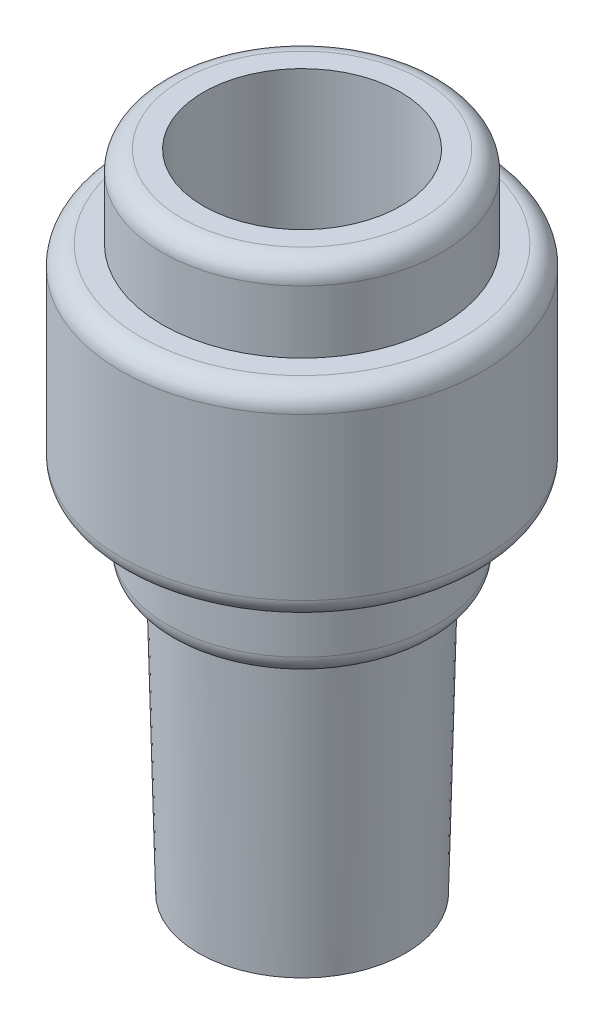
SolidWorks part; units mm, degrees
ref_plane "Front Plane" through (0, 0, 0) normal (0, 0, 1) x (1, 0, 0)
ref_plane "Top Plane" through (0, 0, 0) normal (0, 1, 0) x (1, 0, 0)
ref_plane "Right Plane" through (0, 0, 0) normal (1, 0, 0) x (0, 0, -1)
sketch "Sketch1" plane through (0, 0, 0) normal (0, 1, 0) x (1, 0, 0)
  circle A0 centre (0, 0) radius 3.15
  dimension "D1" = 6.3
extrude "Boss-Extrude1" add sketch "Sketch1" along normal blind 8.5 draft 1.35 draft outward yes
sketch "Sketch2" plane through (0, 8.5, 0) normal (0, 1, 0) x (1, 0, 0)
  circle A0 centre (0, 0) radius 4.075
  dimension "D1" = 8.15
extrude "Boss-Extrude2" add sketch "Sketch2" along normal blind 2.5
sketch "Sketch3" plane through (0, 11, 0) normal (0, 1, 0) x (1, 0, 0)
  circle A0 centre (0, 0) radius 5.5
  dimension "D1" = 11
extrude "Boss-Extrude3" add sketch "Sketch3" along normal blind 6.1
sketch "Sketch4" plane through (0, 17.1, 0) normal (0, 1, 0) x (1, 0, 0)
  circle A0 centre (0, 0) radius 4.25
  dimension "D1" = 8.5
extrude "Boss-Extrude4" add sketch "Sketch4" along normal blind 2.5
sketch "Sketch5" plane through (0, 19.6, 0) normal (0, 1, 0) x (1, 0, 0)
  circle A0 centre (0, 0) radius 3
  dimension "D1" = 6
extrude "Cut-Extrude1" cut sketch "Sketch5" against normal blind 6.5
sketch "Sketch6" plane through (0, 0, 0) normal (0, -1, 0) x (1, 0, 0)
  circle A0 centre (0, 0) radius 1.5
  dimension "D1" = 3
extrude "Cut-Extrude2" cut sketch "Sketch6" against normal up to surface (13.1 mm away) up to face at (0, 13.1, 3)
fillet "Fillet1" radius 0.6 4 edges at (0, 8.5, 4.075) (0, 11, 5.5) (0, 17.1, 5.5) (0, 19.6, 4.25)
